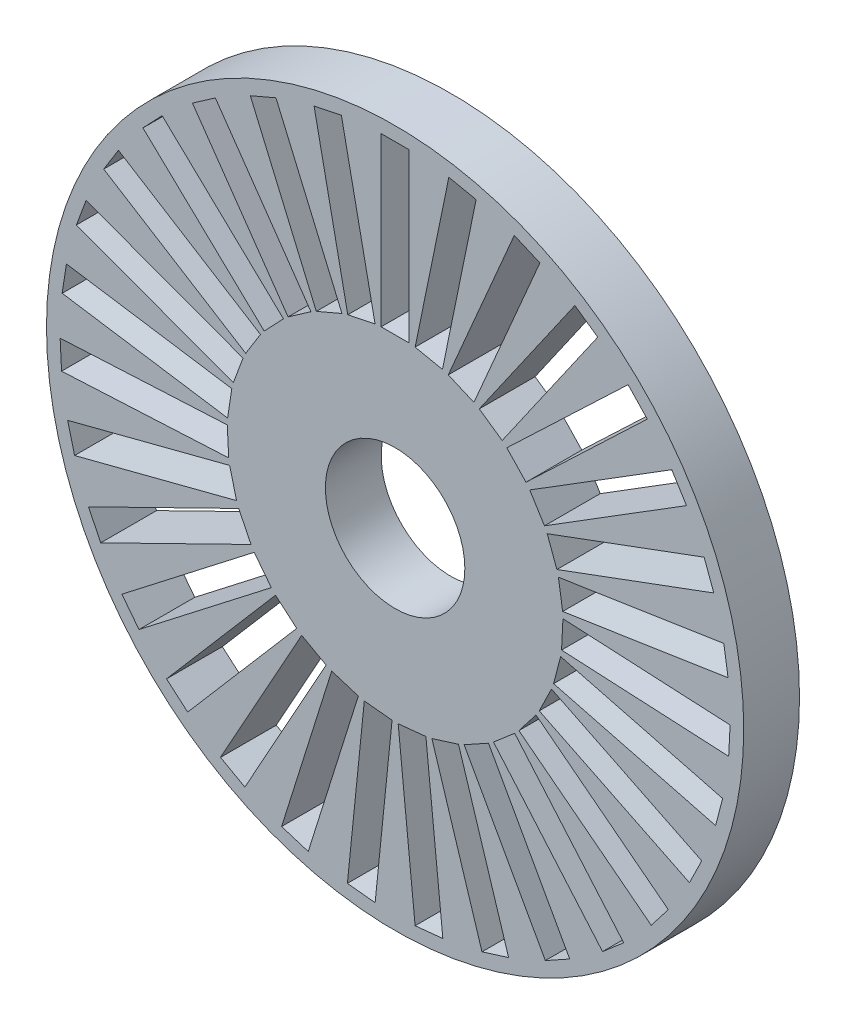
SolidWorks part; units mm, degrees
ref_plane "Ebene vorne" through (0, 0, 0) normal (0, 0, 1) x (1, 0, 0)
ref_plane "Ebene oben" through (0, 0, 0) normal (0, 1, 0) x (1, 0, 0)
ref_plane "Ebene rechts" through (0, 0, 0) normal (1, 0, 0) x (0, 0, -1)
sketch "Skizze1" plane through (0, 0, 0) normal (0, 0, 1) x (1, 0, 0)
  circle A0 centre (0, 0) radius 12.5
  circle A1 centre (0, 0) radius 2.5
  dimension "D1" = 25
  dimension "D2" = 5
extrude "Aufsatz-Linear austragen1" add sketch "Skizze1" along normal blind 2
sketch "Skizze2" plane through (0, 0, 2) normal (0, 0, 1) x (1, 0, 0)
  line L0 (0, 0) -> (0, 31.8323) construction
  line L2 (-0.5, 12) -> (0.5, 12)
  line L3 (-0.5, 12) -> (-0.5, 6)
  line L4 (-0.5, 6) -> (0.5, 6)
  line L5 (0.5, 12) -> (0.5, 6)
  circle A0 centre (0, 0) radius 12.5 construction
  point P8 (0, 6)
  dimension "D1" = 1
  dimension "D2" = 6
  dimension "D3" = 12
extrude "Schnitt-Linear austragen1" cut sketch "Skizze2" against normal up to next (2 mm away)
pattern_circular "Kreismuster1" count 31 over 360 about axis through (0, 0, 0) along (0, 0, 1) of "Schnitt-Linear austragen1"
